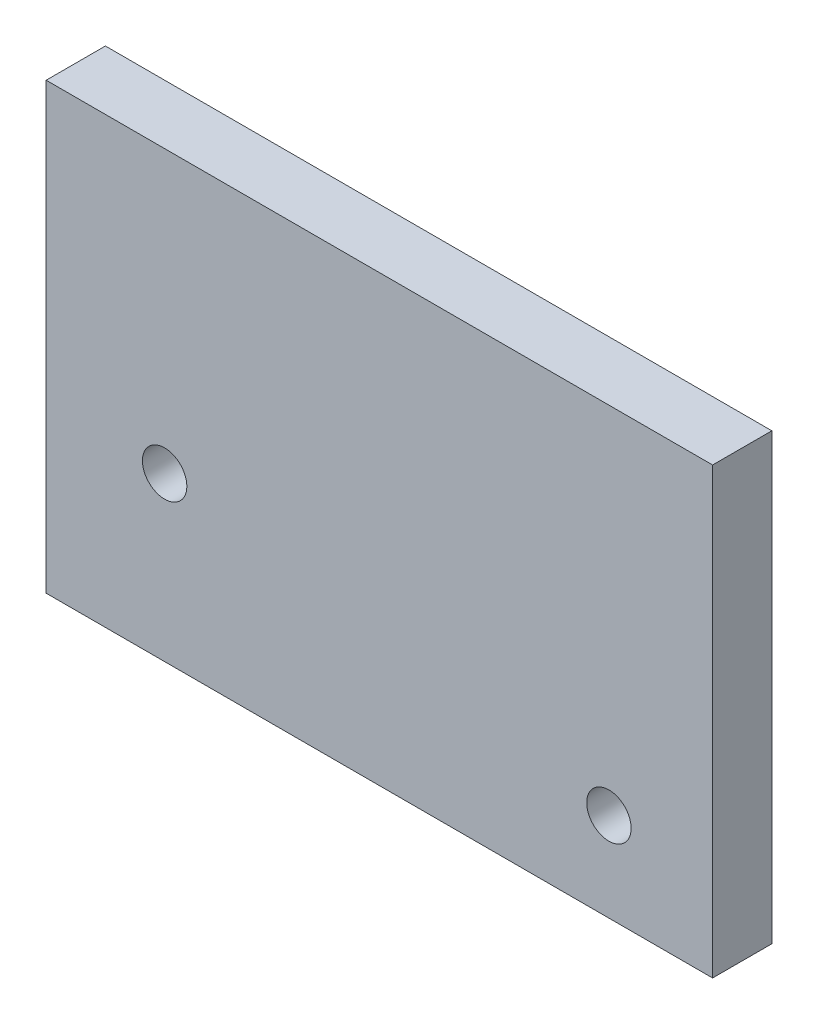
SolidWorks part; units mm, degrees
ref_plane "Front Plane" through (0, 0, 0) normal (0, 0, 1) x (1, 0, 0)
ref_plane "Top Plane" through (0, 0, 0) normal (0, 1, 0) x (1, 0, 0)
ref_plane "Right Plane" through (0, 0, 0) normal (1, 0, 0) x (0, 0, -1)
sketch "Sketch1" plane through (0, 0, 0) normal (0, 0, 1) x (1, 0, 0)
  line L1 (0, 0) -> (45, 0)
  line L2 (0, 0) -> (0, 30)
  line L3 (0, 30) -> (45, 30)
  line L4 (45, 0) -> (45, 30)
  circle A0 centre (38, 6) radius 1.5
  circle A1 centre (8, 11) radius 1.5
  dimension "D3" = 3
  dimension "D1" = 45
  dimension "D2" = 30
  dimension "D4" = 6
  dimension "D5" = 7
  dimension "D6" = 30
  dimension "D7" = 11
extrude "Boss-Extrude1" add sketch "Sketch1" along normal blind 4
